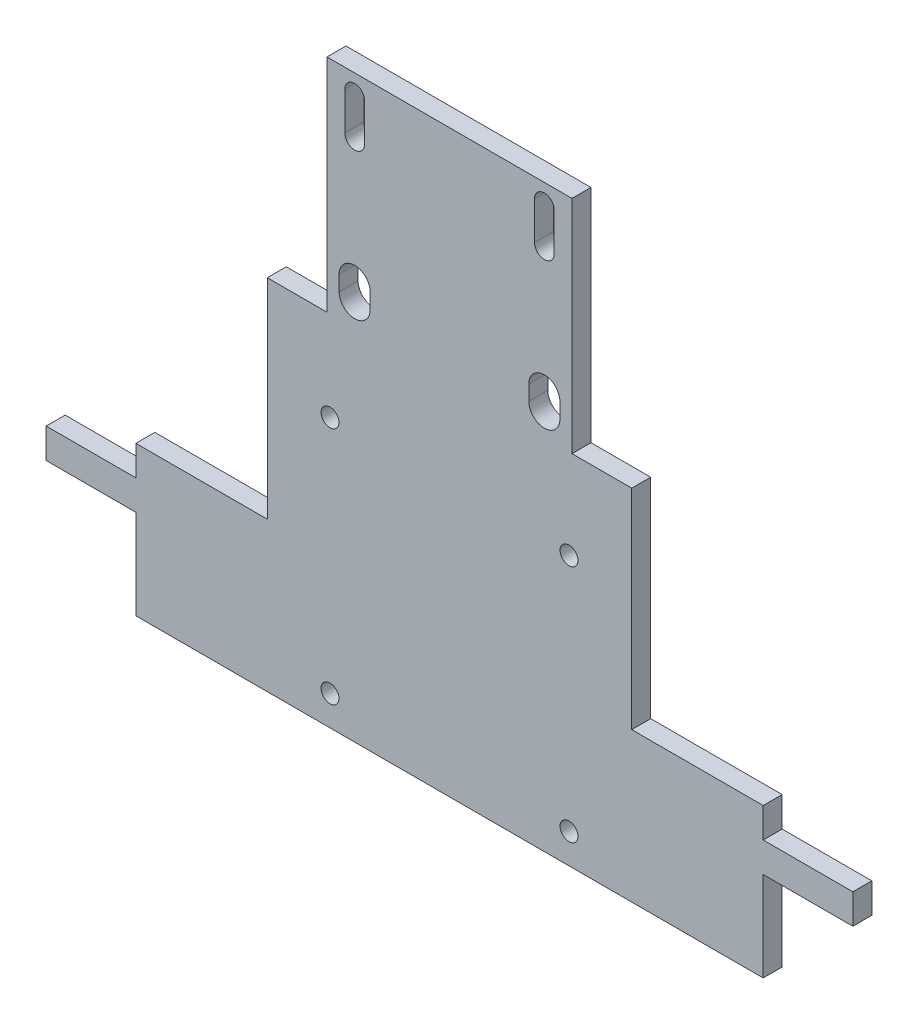
SolidWorks part; units mm, degrees
ref_plane "Front Plane" through (0, 0, 0) normal (0, 0, 1) x (1, 0, 0)
ref_plane "Top Plane" through (0, 0, 0) normal (0, 1, 0) x (1, 0, 0)
ref_plane "Right Plane" through (0, 0, 0) normal (1, 0, 0) x (0, 0, -1)
sketch "Sketch1" plane through (0, 0, 0) normal (0, 0, 1) x (1, 0, 0)
  line L0 (0, 0) -> (10.5, 0)
  line L1 (10.5, 0) -> (10.5, 1.5)
  line L2 (10.5, 1.5) -> (12, 1.5)
  line L3 (12, 1.5) -> (12, 2)
  line L4 (12, 2) -> (10.5, 2)
  line L5 (10.5, 2) -> (10.5, 2.5)
  line L6 (10.5, 2.5) -> (8.3, 2.5)
  line L7 (8.3, 2.5) -> (8.3, 6)
  line L8 (8.3, 6) -> (7.3, 6)
  line L9 (7.3, 6) -> (7.3, 9.7)
  line L10 (7.3, 9.7) -> (3.2, 9.7)
  line L11 (3.2, 9.7) -> (3.2, 6)
  line L12 (3.2, 6) -> (2.2, 6)
  line L13 (2.2, 6) -> (2.2, 2.5)
  line L14 (2.2, 2.5) -> (0, 2.5)
  line L15 (0, 2.5) -> (0, 2)
  line L16 (0, 2) -> (-1.5, 2)
  line L17 (-1.5, 2) -> (-1.5, 1.5)
  line L18 (-1.5, 1.5) -> (0, 1.5)
  line L19 (0, 1.5) -> (0, 0)
  line L20 (3.6625, 9.382) -> (3.6625, 8.747) construction
  line L21 (3.8275, 9.382) -> (3.8275, 8.747)
  line L22 (3.4975, 9.382) -> (3.4975, 8.747)
  line L23 (5.25, 8.3596) -> (5.25, 0.9482) construction
  line L24 (6.8375, 9.382) -> (6.8375, 8.747) construction
  line L25 (6.6725, 9.382) -> (6.6725, 8.747)
  line L26 (7.0025, 9.382) -> (7.0025, 8.747)
  line L27 (3.6625, 6.3975) -> (3.6625, 6.6515) construction
  line L28 (3.4025, 6.3975) -> (3.4025, 6.6515)
  line L29 (3.9225, 6.3975) -> (3.9225, 6.6515)
  line L30 (6.8375, 6.3975) -> (6.8375, 6.6515) construction
  line L31 (7.0975, 6.3975) -> (7.0975, 6.6515)
  line L32 (6.5775, 6.3975) -> (6.5775, 6.6515)
  arc A0 (3.8275, 9.382) -> (3.4975, 9.382) centre (3.6625, 9.382) ccw
  arc A1 (3.4975, 8.747) -> (3.8275, 8.747) centre (3.6625, 8.747) ccw
  circle A2 centre (3.25, 0.5) radius 0.15
  circle A3 centre (7.25, 0.5) radius 0.15
  circle A4 centre (7.25, 4.5) radius 0.15
  circle A5 centre (3.25, 4.5) radius 0.15
  arc A6 (6.6725, 9.382) -> (7.0025, 9.382) centre (6.8375, 9.382) cw
  arc A7 (7.0025, 8.747) -> (6.6725, 8.747) centre (6.8375, 8.747) cw
  arc A8 (3.4025, 6.3975) -> (3.9225, 6.3975) centre (3.6625, 6.3975) ccw
  arc A9 (3.9225, 6.6515) -> (3.4025, 6.6515) centre (3.6625, 6.6515) ccw
  arc A10 (7.0975, 6.3975) -> (6.5775, 6.3975) centre (6.8375, 6.3975) cw
  arc A11 (6.5775, 6.6515) -> (7.0975, 6.6515) centre (6.8375, 6.6515) cw
  point P11 (3.6625, 9.0645)
  point P36 (3.6625, 6.5245)
  point P42 (6.8375, 9.0645)
  point P54 (6.8375, 6.5245)
  dimension "D11" = 0.3
  dimension "D14" = 4
  dimension "D15" = 0.5
  dimension "D16" = 4
  dimension "D17" = 4
  dimension "D20" = 0.165
  dimension "D22" = 0.26
  dimension "D1" = 10.5
  dimension "D2" = 1.5
  dimension "D3" = 1.5
  dimension "D4" = 0.5
  dimension "D5" = 0.5
  dimension "D6" = 2.2
  dimension "D7" = 3.5
  dimension "D8" = 1
  dimension "D9" = 3.7
  dimension "D10" = 0.635
  dimension "D12" = 4
  dimension "D13" = 4
  dimension "D18" = 3.175
  dimension "D19" = 0.318
  dimension "D21" = 2.54
  dimension "D23" = 0.254
extrude "Boss-Extrude1" add sketch "Sketch1" along normal blind 0.3175
scale "Scale1" scale about centroid uniform scaling yes scale factor 10
